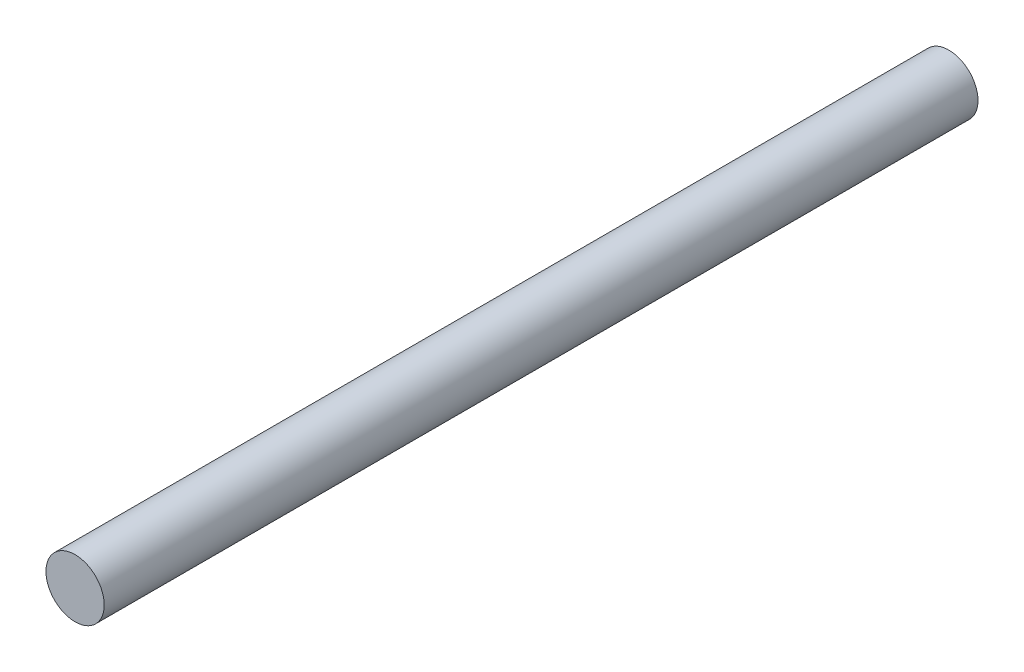
SolidWorks part; units mm, degrees
material "Cast Stainless Steel"
ref_plane "Front Plane" through (0, 0, 0) normal (0, 0, 1) x (1, 0, 0)
ref_plane "Top Plane" through (0, 0, 0) normal (0, 1, 0) x (1, 0, 0)
ref_plane "Right Plane" through (0, 0, 0) normal (1, 0, 0) x (0, 0, -1)
sketch "Sketch1" plane through (0, 0, 0) normal (0, 0, 1) x (1, 0, 0)
  circle A0 centre (0, 0) radius 6.35
  dimension "D1" = 12.7
extrude "Boss-Extrude1" add sketch "Sketch1" along normal blind 190.5
